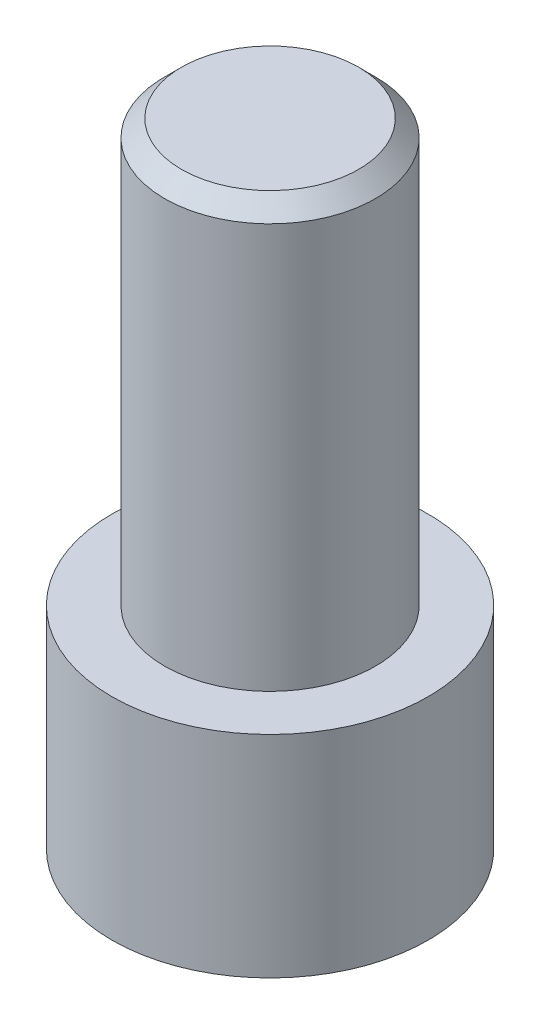
SolidWorks part; units mm, degrees
ref_plane "Front Plane" through (0, 0, 0) normal (0, 0, 1) x (1, 0, 0)
ref_plane "Top Plane" through (0, 0, 0) normal (0, 1, 0) x (1, 0, 0)
ref_plane "Right Plane" through (0, 0, 0) normal (1, 0, 0) x (0, 0, -1)
sketch "Sketch1" plane through (0, 0, 0) normal (0, 1, 0) x (1, 0, 0)
  circle A0 centre (0, 0) radius 4.7625
  dimension "D1" = 9.525
extrude "Boss-Extrude1" add sketch "Sketch1" along normal blind 6.35
sketch "Sketch2" plane through (0, 6.35, 0) normal (0, 1, 0) x (1, 0, 0)
  circle A0 centre (0, 0) radius 3.175
  dimension "D1" = 6.35
extrude "Boss-Extrude2" add sketch "Sketch2" along normal blind 12.7
chamfer "Chamfer1" distance 0.508 angle 45 1 edges at (0, 19.05, 3.175)
sketch "Sketch3" plane through (0, 0, 0) normal (0, -1, 0) x (1, 0, 0)
  line L1 (1.27, 2.1997) -> (-1.27, 2.1997)
  line L2 (-1.27, 2.1997) -> (-2.54, 0)
  line L3 (-2.54, 0) -> (-1.27, -2.1997)
  line L4 (-1.27, -2.1997) -> (1.27, -2.1997)
  line L5 (1.27, -2.1997) -> (2.54, 0)
  line L6 (2.54, 0) -> (1.27, 2.1997)
  circle A0 centre (0, 0) radius 2.1997 construction
  dimension "D1" = 5.08
extrude "Cut-Extrude1" cut sketch "Sketch3" against normal blind 3.81
